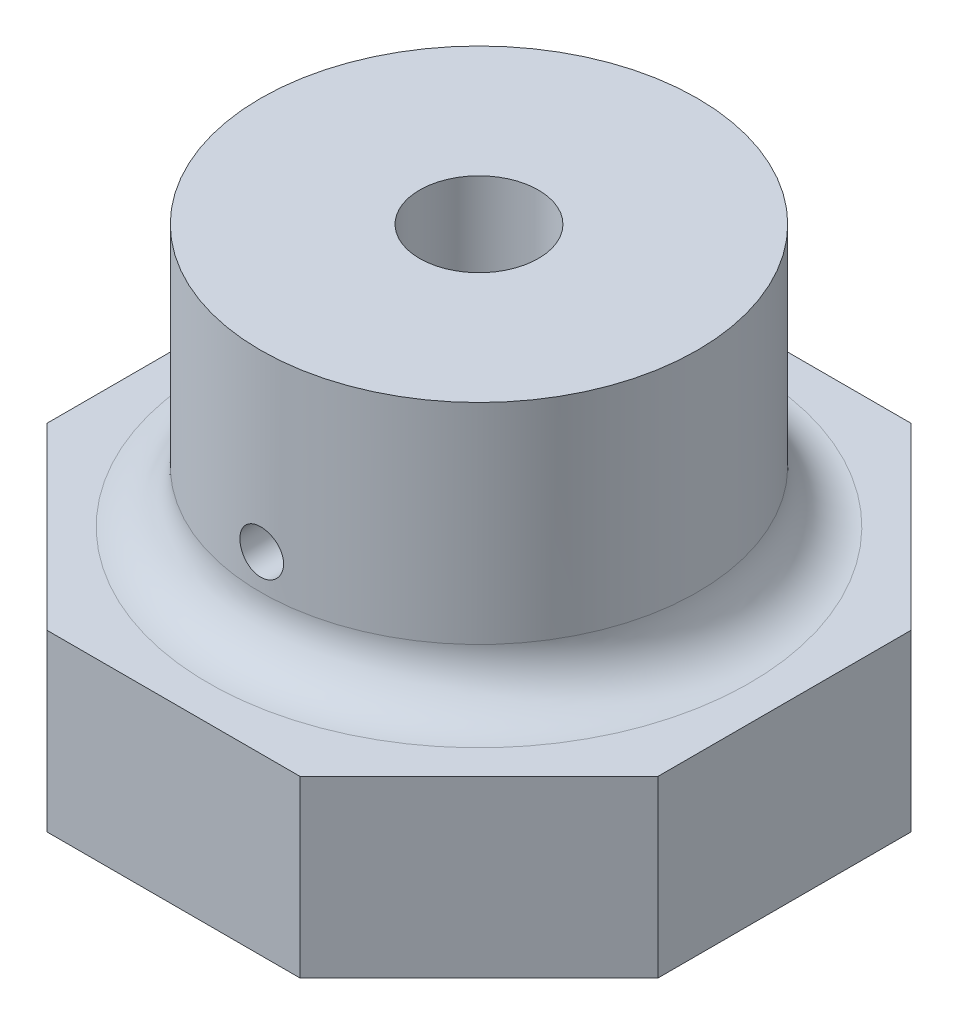
SolidWorks part; units mm, degrees
ref_plane "Front Plane" through (0, 0, 0) normal (0, 0, 1) x (1, 0, 0)
ref_plane "Top Plane" through (0, 0, 0) normal (0, 1, 0) x (1, 0, 0)
ref_plane "Right Plane" through (0, 0, 0) normal (1, 0, 0) x (0, 0, -1)
sketch "Sketch2" plane through (0, 0, 0) normal (0, 1, 0) x (1, 0, 0)
  circle A0 centre (0, 0) radius 12.5
  dimension "D1" = 25
extrude "Boss-Extrude2" add sketch "Sketch2" along normal blind 25
sketch "Sketch3" plane through (0, 25, 0) normal (0, 1, 0) x (1, 0, 0)
  circle A0 centre (0, 0) radius 3.4
  dimension "D1" = 6.8
extrude "Cut-Extrude1" cut sketch "Sketch3" against normal blind 30
sketch "Sketch4" plane through (0, 0, 0) normal (0, 0, 1) x (1, 0, 0)
  line L0 (-12.5, 0) -> (12.5, 0) construction
  circle A0 centre (0, 15) radius 1.25
  dimension "D1" = 2.5
  dimension "D2" = 15
extrude "Cut-Extrude2" cut sketch "Sketch4" against normal blind 2.5 and the other way through all
sketch "Sketch5" plane through (0, 0, 0) normal (0, -1, 0) x (1, 0, 0)
  line L0 (7.2487, -17.5) -> (17.5, -7.2487)
  line L1 (17.5, 7.2487) -> (7.2487, 17.5)
  line L2 (7.2487, 17.5) -> (-7.2487, 17.5)
  line L3 (-7.2487, 17.5) -> (-17.5, 7.2487)
  line L4 (-17.5, 7.2487) -> (-17.5, -7.2487)
  line L5 (-17.5, -7.2487) -> (-7.2487, -17.5)
  line L6 (-7.2487, -17.5) -> (7.2487, -17.5)
  line L7 (17.5, -7.2487) -> (17.5, 7.2487)
  circle A1 centre (0, 0) radius 17.5 construction
extrude "Boss-Extrude3" add sketch "Sketch5" against normal blind 10
fillet "Fillet2" radius 3 1 edges at (0, 10, -12.5)
